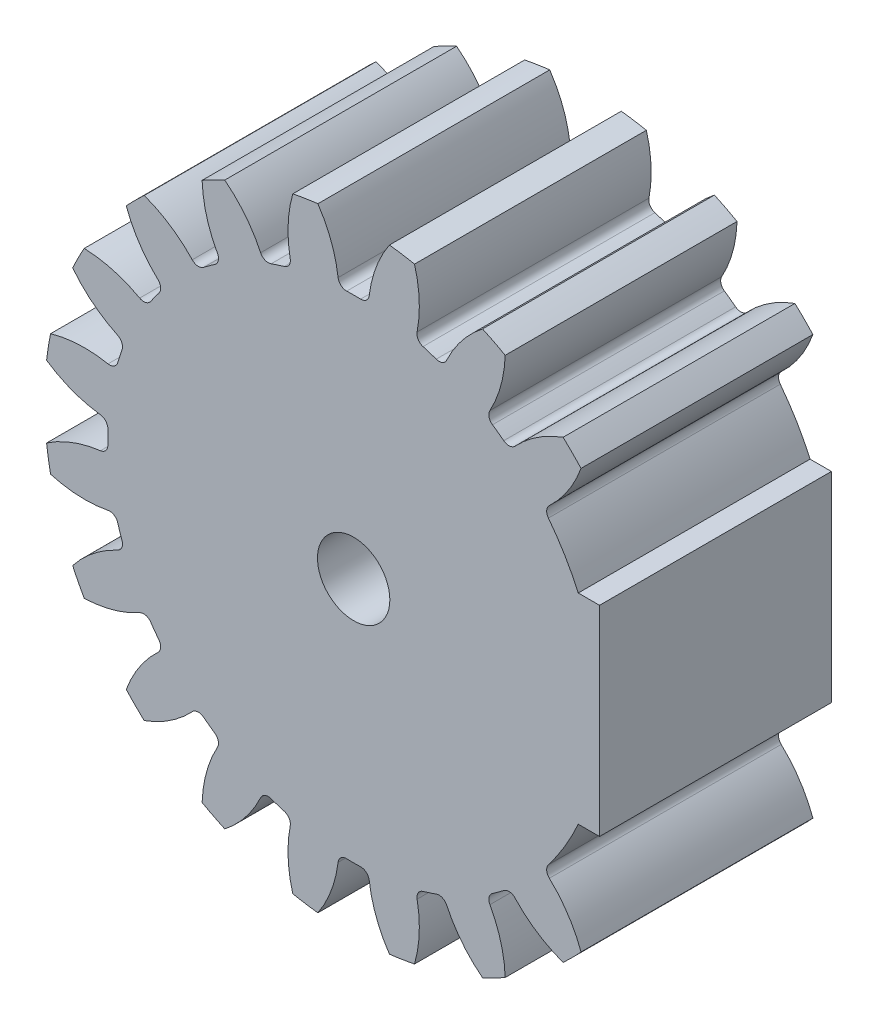
SolidWorks part; units mm, degrees
material "1023 Carbon Steel Sheet (SS)"
ref_plane "Front Plane" through (0, 0, 0) normal (0, 0, 1) x (1, 0, 0)
ref_plane "Top Plane" through (0, 0, 0) normal (0, 1, 0) x (1, 0, 0)
ref_plane "Right Plane" through (0, 0, 0) normal (1, 0, 0) x (0, 0, -1)
sketch "skBase" plane through (0, 0, 0) normal (0, 0, 1) x (1, 0, 0)
  circle A0 centre (0, 0) radius 20
  circle A1 centre (0, 0) radius 22
  circle A2 centre (0, 0) radius 17.5
  dimension "D1" = 40
  dimension "D3" = 4.5
extrude "Base" add sketch "skBase" along normal mid plane 16.5 contours A1
sketch "skToothProfile" plane through (0, 0, 0) normal (0, 0, 1) x (1, 0, 0)
  line L0 (0, 0) -> (0, 22) construction
  line L1 (-1.5692, 19.9383) -> (1.5692, 19.9383) construction
  line L2 (-1.0563, 17.4681) -> (0, 0) construction
  line L3 (0, 15.6271) -> (-2.6287, 22.8493) construction
  line L4 (0, 0) -> (3.4416, 21.7291) construction
  line L5 (1.5692, 19.9383) -> (4.6689, 19.4474) construction
  circle A0 centre (0, 0) radius 22 construction
  arc A1 (-1.0563, 17.4681) -> (-3.258, 22.7681) centre (-9.8105, 16.9387) ccw
  arc A2 (1.0563, 17.4681) -> (3.258, 22.7681) centre (9.8105, 16.9387) cw
  circle A3 centre (0, 0) radius 17.5 construction
  arc A4 (1.0563, 17.4681) -> (-1.0563, 17.4681) centre (0, 0) ccw
  circle A5 centre (0, 0) radius 20 construction
  circle A6 centre (0, 0) radius 22 construction
  circle A7 centre (0, 0) radius 23
  arc A8 (3.258, 22.7681) -> (-3.258, 22.7681) centre (0, 0) ccw
  dimension "D2" = 20
  dimension "D3" = 9
  dimension "D1" = 1
extrude "ToothProfile" cut sketch "skToothProfile" against normal through all and the other way through all
fillet "FilletToothProfile" radius 0.6 2 edges at (1.0563, 17.4681, 0) (-1.0563, 17.4681, 0)
pattern_circular "CirPatternTeeth" count 20 over 360 about axis through (0, 0, 0) along (0, 0, 1) of "ToothProfile", "FilletToothProfile"
sketch "skChaveta" plane through (0, 0, 8.25) normal (0, 0, 1) x (1, 0, 0)
  line L0 (0, 2.575) -> (0, 0) construction
  circle A0 centre (0, 0) radius 2.575
  dimension "D1" = 5.15
extrude "Chaveta" cut sketch "skChaveta" against normal through all
sketch "skRebaixo" plane through (0, 0, 8.25) normal (0, 0, 1) x (1, 0, 0)
  circle A0 centre (0, 0) radius 21.5
  circle A1 centre (0, 0) radius 7.5
  dimension "D1" = 43
  dimension "D2" = 15
sketch "Sketch4" plane through (0, 0, -8.25) normal (0, 0, -1) x (-1, 0, 0)
  circle A0 centre (0, 0) radius 17.5
  arc A5 (-2.5459, 21.8522) -> (-4.3314, 21.5694) centre (0, 0) ccw
  arc A6 (-2.5459, 21.8522) -> (-4.3314, 21.5694) centre (0, 0) ccw
  arc A7 (-18.0189, -1.107) -> (-21.8522, -2.5459) centre (-16.9387, -9.8105) ccw
  arc A8 (-18.0189, -1.107) -> (-21.8522, -2.5459) centre (-16.9387, -9.8105) ccw
  arc A9 (-21.5694, -4.3314) -> (-17.4791, -4.5153) centre (-19.1413, 4.096) ccw
  arc A10 (-21.5694, -4.3314) -> (-17.4791, -4.5153) centre (-19.1413, 4.096) ccw
  arc A127 (-19.996, -9.174) -> (-19.1752, -10.7848) centre (0, 0) ccw
  arc A128 (-19.996, -9.174) -> (-19.1752, -10.7848) centre (0, 0) ccw
  arc A129 (-16.1824, -14.904) -> (-14.904, -16.1824) centre (0, 0) ccw
  arc A130 (-16.1824, -14.904) -> (-14.904, -16.1824) centre (0, 0) ccw
  arc A131 (-10.7848, -19.1752) -> (-9.174, -19.996) centre (0, 0) ccw
  arc A132 (-10.7848, -19.1752) -> (-9.174, -19.996) centre (0, 0) ccw
  arc A133 (-4.3314, -21.5694) -> (-2.5459, -21.8522) centre (0, 0) ccw
  arc A134 (-4.3314, -21.5694) -> (-2.5459, -21.8522) centre (0, 0) ccw
  arc A135 (2.5459, -21.8522) -> (4.3314, -21.5694) centre (0, 0) ccw
  arc A136 (2.5459, -21.8522) -> (4.3314, -21.5694) centre (0, 0) ccw
  arc A137 (9.174, -19.996) -> (10.7848, -19.1752) centre (0, 0) ccw
  arc A138 (9.174, -19.996) -> (10.7848, -19.1752) centre (0, 0) ccw
  arc A139 (14.904, -16.1824) -> (16.1824, -14.904) centre (0, 0) ccw
  arc A140 (14.904, -16.1824) -> (16.1824, -14.904) centre (0, 0) ccw
  arc A141 (19.1752, -10.7848) -> (19.996, -9.174) centre (0, 0) ccw
  arc A142 (19.1752, -10.7848) -> (19.996, -9.174) centre (0, 0) ccw
  arc A143 (21.5694, -4.3314) -> (21.8522, -2.5459) centre (0, 0) ccw
  arc A144 (21.5694, -4.3314) -> (21.8522, -2.5459) centre (0, 0) ccw
  arc A145 (21.8522, 2.5459) -> (21.5694, 4.3314) centre (0, 0) ccw
  arc A146 (21.8522, 2.5459) -> (21.5694, 4.3314) centre (0, 0) ccw
  arc A147 (19.996, 9.174) -> (19.1752, 10.7848) centre (0, 0) ccw
  arc A148 (19.996, 9.174) -> (19.1752, 10.7848) centre (0, 0) ccw
  arc A149 (16.1824, 14.904) -> (14.904, 16.1824) centre (0, 0) ccw
  arc A150 (16.1824, 14.904) -> (14.904, 16.1824) centre (0, 0) ccw
  arc A151 (10.7848, 19.1752) -> (9.174, 19.996) centre (0, 0) ccw
  arc A152 (10.7848, 19.1752) -> (9.174, 19.996) centre (0, 0) ccw
  arc A153 (4.3314, 21.5694) -> (2.5459, 21.8522) centre (0, 0) ccw
  arc A154 (4.3314, 21.5694) -> (2.5459, 21.8522) centre (0, 0) ccw
  arc A155 (-9.174, 19.996) -> (-10.7848, 19.1752) centre (0, 0) ccw
  arc A156 (-9.174, 19.996) -> (-10.7848, 19.1752) centre (0, 0) ccw
  arc A157 (-14.904, 16.1824) -> (-16.1824, 14.904) centre (0, 0) ccw
  arc A158 (-14.904, 16.1824) -> (-16.1824, 14.904) centre (0, 0) ccw
  arc A159 (-19.1752, 10.7848) -> (-19.996, 9.174) centre (0, 0) ccw
  arc A160 (-19.1752, 10.7848) -> (-19.996, 9.174) centre (0, 0) ccw
  arc A161 (-21.5694, 4.3314) -> (-21.8522, 2.5459) centre (0, 0) ccw
  arc A162 (-21.5694, 4.3314) -> (-21.8522, 2.5459) centre (0, 0) ccw
  arc A163 (-4.3314, 21.5694) -> (-4.5153, 17.4791) centre (4.096, 19.1413) ccw
  arc A164 (-4.3314, 21.5694) -> (-4.5153, 17.4791) centre (4.096, 19.1413) ccw
  arc A165 (-4.9352, 16.7897) -> (-4.5153, 17.4791) centre (-5.1044, 17.3653) ccw
  arc A166 (-4.9352, 16.7897) -> (-4.5153, 17.4791) centre (-5.1044, 17.3653) ccw
  arc A167 (-4.9352, 16.7897) -> (-5.8761, 16.484) centre (0, 0) ccw
  arc A168 (-4.9352, 16.7897) -> (-5.8761, 16.484) centre (0, 0) ccw
  arc A169 (-6.621, 16.7949) -> (-5.8761, 16.484) centre (-6.0775, 17.0492) ccw
  arc A170 (-6.621, 16.7949) -> (-5.8761, 16.484) centre (-6.0775, 17.0492) ccw
  arc A171 (-6.621, 16.7949) -> (-9.174, 19.996) centre (-14.5647, 13.0781) ccw
  arc A172 (-6.621, 16.7949) -> (-9.174, 19.996) centre (-14.5647, 13.0781) ccw
  arc A173 (-10.7848, 19.1752) -> (-9.6956, 15.2283) centre (-2.0195, 19.4702) ccw
  arc A174 (-10.7848, 19.1752) -> (-9.6956, 15.2283) centre (-2.0195, 19.4702) ccw
  arc A175 (-9.882, 14.4429) -> (-9.6956, 15.2283) centre (-10.2208, 14.9381) ccw
  arc A176 (-9.882, 14.4429) -> (-9.6956, 15.2283) centre (-10.2208, 14.9381) ccw
  arc A177 (-9.882, 14.4429) -> (-10.6823, 13.8614) centre (0, 0) ccw
  arc A178 (-9.882, 14.4429) -> (-10.6823, 13.8614) centre (0, 0) ccw
  arc A179 (-11.4868, 13.9269) -> (-10.6823, 13.8614) centre (-11.0486, 14.3366) ccw
  arc A180 (-11.4868, 13.9269) -> (-10.6823, 13.8614) centre (-11.0486, 14.3366) ccw
  arc A181 (-11.4868, 13.9269) -> (-14.904, 16.1824) centre (-17.8932, 7.9372) ccw
  arc A182 (-11.4868, 13.9269) -> (-14.904, 16.1824) centre (-17.8932, 7.9372) ccw
  arc A183 (-16.1824, 14.904) -> (-13.9269, 11.4868) centre (-7.9372, 17.8932) ccw
  arc A184 (-16.1824, 14.904) -> (-13.9269, 11.4868) centre (-7.9372, 17.8932) ccw
  arc A185 (-13.8614, 10.6823) -> (-13.9269, 11.4868) centre (-14.3366, 11.0486) ccw
  arc A186 (-13.8614, 10.6823) -> (-13.9269, 11.4868) centre (-14.3366, 11.0486) ccw
  arc A187 (-13.8614, 10.6823) -> (-14.4429, 9.882) centre (0, 0) ccw
  arc A188 (-13.8614, 10.6823) -> (-14.4429, 9.882) centre (0, 0) ccw
  arc A189 (-15.2283, 9.6956) -> (-14.4429, 9.882) centre (-14.9381, 10.2208) ccw
  arc A190 (-15.2283, 9.6956) -> (-14.4429, 9.882) centre (-14.9381, 10.2208) ccw
  arc A191 (-15.2283, 9.6956) -> (-19.1752, 10.7848) centre (-19.4702, 2.0195) ccw
  arc A192 (-15.2283, 9.6956) -> (-19.1752, 10.7848) centre (-19.4702, 2.0195) ccw
  arc A193 (-19.996, 9.174) -> (-16.7949, 6.621) centre (-13.0781, 14.5647) ccw
  arc A194 (-19.996, 9.174) -> (-16.7949, 6.621) centre (-13.0781, 14.5647) ccw
  arc A195 (-16.484, 5.8761) -> (-16.7949, 6.621) centre (-17.0492, 6.0775) ccw
  arc A196 (-16.484, 5.8761) -> (-16.7949, 6.621) centre (-17.0492, 6.0775) ccw
  arc A197 (-16.484, 5.8761) -> (-16.7897, 4.9352) centre (0, 0) ccw
  arc A198 (-16.484, 5.8761) -> (-16.7897, 4.9352) centre (0, 0) ccw
  arc A199 (-17.4791, 4.5153) -> (-16.7897, 4.9352) centre (-17.3653, 5.1044) ccw
  arc A200 (-17.4791, 4.5153) -> (-16.7897, 4.9352) centre (-17.3653, 5.1044) ccw
  arc A201 (-17.4791, 4.5153) -> (-21.5694, 4.3314) centre (-19.1413, -4.096) ccw
  arc A202 (-17.4791, 4.5153) -> (-21.5694, 4.3314) centre (-19.1413, -4.096) ccw
  arc A203 (-21.8522, 2.5459) -> (-18.0189, 1.107) centre (-16.9387, 9.8105) ccw
  arc A204 (-21.8522, 2.5459) -> (-18.0189, 1.107) centre (-16.9387, 9.8105) ccw
  arc A205 (-17.493, 0.4946) -> (-18.0189, 1.107) centre (-18.0928, 0.5116) ccw
  arc A206 (-17.493, 0.4946) -> (-18.0189, 1.107) centre (-18.0928, 0.5116) ccw
  arc A207 (-17.493, 0.4946) -> (-17.493, -0.4946) centre (0, 0) ccw
  arc A208 (-17.493, 0.4946) -> (-17.493, -0.4946) centre (0, 0) ccw
  arc A209 (-18.0189, -1.107) -> (-17.493, -0.4946) centre (-18.0928, -0.5116) ccw
  arc A210 (-18.0189, -1.107) -> (-17.493, -0.4946) centre (-18.0928, -0.5116) ccw
  arc A211 (-16.7897, -4.9352) -> (-17.4791, -4.5153) centre (-17.3653, -5.1044) ccw
  arc A212 (-16.7897, -4.9352) -> (-17.4791, -4.5153) centre (-17.3653, -5.1044) ccw
  arc A213 (-16.7897, -4.9352) -> (-16.484, -5.8761) centre (0, 0) ccw
  arc A214 (-16.7897, -4.9352) -> (-16.484, -5.8761) centre (0, 0) ccw
  arc A215 (-16.7949, -6.621) -> (-16.484, -5.8761) centre (-17.0492, -6.0775) ccw
  arc A216 (-16.7949, -6.621) -> (-16.484, -5.8761) centre (-17.0492, -6.0775) ccw
  arc A217 (-16.7949, -6.621) -> (-19.996, -9.174) centre (-13.0781, -14.5647) ccw
  arc A218 (-16.7949, -6.621) -> (-19.996, -9.174) centre (-13.0781, -14.5647) ccw
  arc A219 (-19.1752, -10.7848) -> (-15.2283, -9.6956) centre (-19.4702, -2.0195) ccw
  arc A220 (-19.1752, -10.7848) -> (-15.2283, -9.6956) centre (-19.4702, -2.0195) ccw
  arc A221 (-14.4429, -9.882) -> (-15.2283, -9.6956) centre (-14.9381, -10.2208) ccw
  arc A222 (-14.4429, -9.882) -> (-15.2283, -9.6956) centre (-14.9381, -10.2208) ccw
  arc A223 (-14.4429, -9.882) -> (-13.8614, -10.6823) centre (0, 0) ccw
  arc A224 (-14.4429, -9.882) -> (-13.8614, -10.6823) centre (0, 0) ccw
  arc A225 (-13.9269, -11.4868) -> (-13.8614, -10.6823) centre (-14.3366, -11.0486) ccw
  arc A226 (-13.9269, -11.4868) -> (-13.8614, -10.6823) centre (-14.3366, -11.0486) ccw
  arc A227 (-13.9269, -11.4868) -> (-16.1824, -14.904) centre (-7.9372, -17.8932) ccw
  arc A228 (-13.9269, -11.4868) -> (-16.1824, -14.904) centre (-7.9372, -17.8932) ccw
  arc A229 (-14.904, -16.1824) -> (-11.4868, -13.9269) centre (-17.8932, -7.9372) ccw
  arc A230 (-14.904, -16.1824) -> (-11.4868, -13.9269) centre (-17.8932, -7.9372) ccw
  arc A231 (-10.6823, -13.8614) -> (-11.4868, -13.9269) centre (-11.0486, -14.3366) ccw
  arc A232 (-10.6823, -13.8614) -> (-11.4868, -13.9269) centre (-11.0486, -14.3366) ccw
  arc A233 (-10.6823, -13.8614) -> (-9.882, -14.4429) centre (0, 0) ccw
  arc A234 (-10.6823, -13.8614) -> (-9.882, -14.4429) centre (0, 0) ccw
  arc A235 (-9.6956, -15.2283) -> (-9.882, -14.4429) centre (-10.2208, -14.9381) ccw
  arc A236 (-9.6956, -15.2283) -> (-9.882, -14.4429) centre (-10.2208, -14.9381) ccw
  arc A237 (-9.6956, -15.2283) -> (-10.7848, -19.1752) centre (-2.0195, -19.4702) ccw
  arc A238 (-9.6956, -15.2283) -> (-10.7848, -19.1752) centre (-2.0195, -19.4702) ccw
  arc A239 (-9.174, -19.996) -> (-6.621, -16.7949) centre (-14.5647, -13.0781) ccw
  arc A240 (-9.174, -19.996) -> (-6.621, -16.7949) centre (-14.5647, -13.0781) ccw
  arc A241 (-5.8761, -16.484) -> (-6.621, -16.7949) centre (-6.0775, -17.0492) ccw
  arc A242 (-5.8761, -16.484) -> (-6.621, -16.7949) centre (-6.0775, -17.0492) ccw
  arc A243 (-5.8761, -16.484) -> (-4.9352, -16.7897) centre (0, 0) ccw
  arc A244 (-5.8761, -16.484) -> (-4.9352, -16.7897) centre (0, 0) ccw
  arc A245 (-4.5153, -17.4791) -> (-4.9352, -16.7897) centre (-5.1044, -17.3653) ccw
  arc A246 (-4.5153, -17.4791) -> (-4.9352, -16.7897) centre (-5.1044, -17.3653) ccw
  arc A247 (-4.5153, -17.4791) -> (-4.3314, -21.5694) centre (4.096, -19.1413) ccw
  arc A248 (-4.5153, -17.4791) -> (-4.3314, -21.5694) centre (4.096, -19.1413) ccw
  arc A249 (-2.5459, -21.8522) -> (-1.107, -18.0189) centre (-9.8105, -16.9387) ccw
  arc A250 (-2.5459, -21.8522) -> (-1.107, -18.0189) centre (-9.8105, -16.9387) ccw
  arc A251 (-0.4946, -17.493) -> (-1.107, -18.0189) centre (-0.5116, -18.0928) ccw
  arc A252 (-0.4946, -17.493) -> (-1.107, -18.0189) centre (-0.5116, -18.0928) ccw
  arc A253 (-0.4946, -17.493) -> (0.4946, -17.493) centre (0, 0) ccw
  arc A254 (-0.4946, -17.493) -> (0.4946, -17.493) centre (0, 0) ccw
  arc A255 (1.107, -18.0189) -> (0.4946, -17.493) centre (0.5116, -18.0928) ccw
  arc A256 (1.107, -18.0189) -> (0.4946, -17.493) centre (0.5116, -18.0928) ccw
  arc A257 (1.107, -18.0189) -> (2.5459, -21.8522) centre (9.8105, -16.9387) ccw
  arc A258 (1.107, -18.0189) -> (2.5459, -21.8522) centre (9.8105, -16.9387) ccw
  arc A259 (4.3314, -21.5694) -> (4.5153, -17.4791) centre (-4.096, -19.1413) ccw
  arc A260 (4.3314, -21.5694) -> (4.5153, -17.4791) centre (-4.096, -19.1413) ccw
  arc A261 (4.9352, -16.7897) -> (4.5153, -17.4791) centre (5.1044, -17.3653) ccw
  arc A262 (4.9352, -16.7897) -> (4.5153, -17.4791) centre (5.1044, -17.3653) ccw
  arc A263 (4.9352, -16.7897) -> (5.8761, -16.484) centre (0, 0) ccw
  arc A264 (4.9352, -16.7897) -> (5.8761, -16.484) centre (0, 0) ccw
  arc A265 (6.621, -16.7949) -> (5.8761, -16.484) centre (6.0775, -17.0492) ccw
  arc A266 (6.621, -16.7949) -> (5.8761, -16.484) centre (6.0775, -17.0492) ccw
  arc A267 (6.621, -16.7949) -> (9.174, -19.996) centre (14.5647, -13.0781) ccw
  arc A268 (6.621, -16.7949) -> (9.174, -19.996) centre (14.5647, -13.0781) ccw
  arc A269 (10.7848, -19.1752) -> (9.6956, -15.2283) centre (2.0195, -19.4702) ccw
  arc A270 (10.7848, -19.1752) -> (9.6956, -15.2283) centre (2.0195, -19.4702) ccw
  arc A271 (9.882, -14.4429) -> (9.6956, -15.2283) centre (10.2208, -14.9381) ccw
  arc A272 (9.882, -14.4429) -> (9.6956, -15.2283) centre (10.2208, -14.9381) ccw
  arc A273 (9.882, -14.4429) -> (10.6823, -13.8614) centre (0, 0) ccw
  arc A274 (9.882, -14.4429) -> (10.6823, -13.8614) centre (0, 0) ccw
  arc A275 (11.4868, -13.9269) -> (10.6823, -13.8614) centre (11.0486, -14.3366) ccw
  arc A276 (11.4868, -13.9269) -> (10.6823, -13.8614) centre (11.0486, -14.3366) ccw
  arc A277 (11.4868, -13.9269) -> (14.904, -16.1824) centre (17.8932, -7.9372) ccw
  arc A278 (11.4868, -13.9269) -> (14.904, -16.1824) centre (17.8932, -7.9372) ccw
  arc A279 (16.1824, -14.904) -> (13.9269, -11.4868) centre (7.9372, -17.8932) ccw
  arc A280 (16.1824, -14.904) -> (13.9269, -11.4868) centre (7.9372, -17.8932) ccw
  arc A281 (13.8614, -10.6823) -> (13.9269, -11.4868) centre (14.3366, -11.0486) ccw
  arc A282 (13.8614, -10.6823) -> (13.9269, -11.4868) centre (14.3366, -11.0486) ccw
  arc A283 (13.8614, -10.6823) -> (14.4429, -9.882) centre (0, 0) ccw
  arc A284 (13.8614, -10.6823) -> (14.4429, -9.882) centre (0, 0) ccw
  arc A285 (15.2283, -9.6956) -> (14.4429, -9.882) centre (14.9381, -10.2208) ccw
  arc A286 (15.2283, -9.6956) -> (14.4429, -9.882) centre (14.9381, -10.2208) ccw
  arc A287 (15.2283, -9.6956) -> (19.1752, -10.7848) centre (19.4702, -2.0195) ccw
  arc A288 (15.2283, -9.6956) -> (19.1752, -10.7848) centre (19.4702, -2.0195) ccw
  arc A289 (19.996, -9.174) -> (16.7949, -6.621) centre (13.0781, -14.5647) ccw
  arc A290 (19.996, -9.174) -> (16.7949, -6.621) centre (13.0781, -14.5647) ccw
  arc A291 (16.484, -5.8761) -> (16.7949, -6.621) centre (17.0492, -6.0775) ccw
  arc A292 (16.484, -5.8761) -> (16.7949, -6.621) centre (17.0492, -6.0775) ccw
  arc A293 (16.484, -5.8761) -> (16.7897, -4.9352) centre (0, 0) ccw
  arc A294 (16.484, -5.8761) -> (16.7897, -4.9352) centre (0, 0) ccw
  arc A295 (17.4791, -4.5153) -> (16.7897, -4.9352) centre (17.3653, -5.1044) ccw
  arc A296 (17.4791, -4.5153) -> (16.7897, -4.9352) centre (17.3653, -5.1044) ccw
  arc A297 (17.4791, -4.5153) -> (21.5694, -4.3314) centre (19.1413, 4.096) ccw
  arc A298 (17.4791, -4.5153) -> (21.5694, -4.3314) centre (19.1413, 4.096) ccw
  arc A299 (21.8522, -2.5459) -> (18.0189, -1.107) centre (16.9387, -9.8105) ccw
  arc A300 (21.8522, -2.5459) -> (18.0189, -1.107) centre (16.9387, -9.8105) ccw
  arc A301 (17.493, -0.4946) -> (18.0189, -1.107) centre (18.0928, -0.5116) ccw
  arc A302 (17.493, -0.4946) -> (18.0189, -1.107) centre (18.0928, -0.5116) ccw
  arc A303 (17.493, -0.4946) -> (17.493, 0.4946) centre (0, 0) ccw
  arc A304 (17.493, -0.4946) -> (17.493, 0.4946) centre (0, 0) ccw
  arc A305 (18.0189, 1.107) -> (17.493, 0.4946) centre (18.0928, 0.5116) ccw
  arc A306 (18.0189, 1.107) -> (17.493, 0.4946) centre (18.0928, 0.5116) ccw
  arc A307 (18.0189, 1.107) -> (21.8522, 2.5459) centre (16.9387, 9.8105) ccw
  arc A308 (18.0189, 1.107) -> (21.8522, 2.5459) centre (16.9387, 9.8105) ccw
  arc A309 (21.5694, 4.3314) -> (17.4791, 4.5153) centre (19.1413, -4.096) ccw
  arc A310 (21.5694, 4.3314) -> (17.4791, 4.5153) centre (19.1413, -4.096) ccw
  arc A311 (-21.8522, -2.5459) -> (-21.5694, -4.3314) centre (0, 0) ccw
  arc A312 (-21.8522, -2.5459) -> (-21.5694, -4.3314) centre (0, 0) ccw
  arc A313 (16.7897, 4.9352) -> (17.4791, 4.5153) centre (17.3653, 5.1044) ccw
  arc A314 (16.7897, 4.9352) -> (17.4791, 4.5153) centre (17.3653, 5.1044) ccw
  arc A315 (16.7897, 4.9352) -> (16.484, 5.8761) centre (0, 0) ccw
  arc A316 (16.7897, 4.9352) -> (16.484, 5.8761) centre (0, 0) ccw
  arc A317 (16.7949, 6.621) -> (16.484, 5.8761) centre (17.0492, 6.0775) ccw
  arc A318 (16.7949, 6.621) -> (16.484, 5.8761) centre (17.0492, 6.0775) ccw
  arc A319 (16.7949, 6.621) -> (19.996, 9.174) centre (13.0781, 14.5647) ccw
  arc A320 (16.7949, 6.621) -> (19.996, 9.174) centre (13.0781, 14.5647) ccw
  arc A321 (19.1752, 10.7848) -> (15.2283, 9.6956) centre (19.4702, 2.0195) ccw
  arc A322 (19.1752, 10.7848) -> (15.2283, 9.6956) centre (19.4702, 2.0195) ccw
  arc A323 (14.4429, 9.882) -> (15.2283, 9.6956) centre (14.9381, 10.2208) ccw
  arc A324 (14.4429, 9.882) -> (15.2283, 9.6956) centre (14.9381, 10.2208) ccw
  arc A325 (14.4429, 9.882) -> (13.8614, 10.6823) centre (0, 0) ccw
  arc A326 (14.4429, 9.882) -> (13.8614, 10.6823) centre (0, 0) ccw
  arc A327 (13.9269, 11.4868) -> (13.8614, 10.6823) centre (14.3366, 11.0486) ccw
  arc A328 (13.9269, 11.4868) -> (13.8614, 10.6823) centre (14.3366, 11.0486) ccw
  arc A329 (13.9269, 11.4868) -> (16.1824, 14.904) centre (7.9372, 17.8932) ccw
  arc A330 (13.9269, 11.4868) -> (16.1824, 14.904) centre (7.9372, 17.8932) ccw
  arc A331 (14.904, 16.1824) -> (11.4868, 13.9269) centre (17.8932, 7.9372) ccw
  arc A332 (14.904, 16.1824) -> (11.4868, 13.9269) centre (17.8932, 7.9372) ccw
  arc A333 (10.6823, 13.8614) -> (11.4868, 13.9269) centre (11.0486, 14.3366) ccw
  arc A334 (10.6823, 13.8614) -> (11.4868, 13.9269) centre (11.0486, 14.3366) ccw
  arc A335 (10.6823, 13.8614) -> (9.882, 14.4429) centre (0, 0) ccw
  arc A336 (10.6823, 13.8614) -> (9.882, 14.4429) centre (0, 0) ccw
  arc A337 (9.6956, 15.2283) -> (9.882, 14.4429) centre (10.2208, 14.9381) ccw
  arc A338 (9.6956, 15.2283) -> (9.882, 14.4429) centre (10.2208, 14.9381) ccw
  arc A339 (9.6956, 15.2283) -> (10.7848, 19.1752) centre (2.0195, 19.4702) ccw
  arc A340 (9.6956, 15.2283) -> (10.7848, 19.1752) centre (2.0195, 19.4702) ccw
  arc A341 (9.174, 19.996) -> (6.621, 16.7949) centre (14.5647, 13.0781) ccw
  arc A342 (9.174, 19.996) -> (6.621, 16.7949) centre (14.5647, 13.0781) ccw
  arc A343 (5.8761, 16.484) -> (6.621, 16.7949) centre (6.0775, 17.0492) ccw
  arc A344 (5.8761, 16.484) -> (6.621, 16.7949) centre (6.0775, 17.0492) ccw
  arc A345 (5.8761, 16.484) -> (4.9352, 16.7897) centre (0, 0) ccw
  arc A346 (5.8761, 16.484) -> (4.9352, 16.7897) centre (0, 0) ccw
  arc A347 (4.5153, 17.4791) -> (4.9352, 16.7897) centre (5.1044, 17.3653) ccw
  arc A348 (4.5153, 17.4791) -> (4.9352, 16.7897) centre (5.1044, 17.3653) ccw
  arc A349 (4.5153, 17.4791) -> (4.3314, 21.5694) centre (-4.096, 19.1413) ccw
  arc A350 (4.5153, 17.4791) -> (4.3314, 21.5694) centre (-4.096, 19.1413) ccw
  arc A351 (2.5459, 21.8522) -> (1.107, 18.0189) centre (9.8105, 16.9387) ccw
  arc A352 (2.5459, 21.8522) -> (1.107, 18.0189) centre (9.8105, 16.9387) ccw
  arc A353 (0.4946, 17.493) -> (1.107, 18.0189) centre (0.5116, 18.0928) ccw
  arc A354 (0.4946, 17.493) -> (1.107, 18.0189) centre (0.5116, 18.0928) ccw
  arc A355 (0.4946, 17.493) -> (-0.4946, 17.493) centre (0, 0) ccw
  arc A356 (0.4946, 17.493) -> (-0.4946, 17.493) centre (0, 0) ccw
  arc A357 (-1.107, 18.0189) -> (-0.4946, 17.493) centre (-0.5116, 18.0928) ccw
  arc A358 (-1.107, 18.0189) -> (-0.4946, 17.493) centre (-0.5116, 18.0928) ccw
  arc A359 (-1.107, 18.0189) -> (-2.5459, 21.8522) centre (-9.8105, 16.9387) ccw
  arc A360 (-1.107, 18.0189) -> (-2.5459, 21.8522) centre (-9.8105, 16.9387) ccw
  dimension "D1" = 0
sketch "Sketch6" plane through (0, 0, -8.25) normal (0, 0, -1) x (-1, 0, 0)
  circle A0 centre (0, 0) radius 20 construction
  dimension "D1" = 40
sketch "Sketch7" plane through (0, 0, -8.25) normal (0, 0, -1) x (-1, 0, 0)
  circle A0 centre (0, 0) radius 17.5
  arc A120 (-2.5459, 21.8522) -> (-4.3314, 21.5694) centre (0, 0) ccw
  arc A121 (-4.3314, 21.5694) -> (-4.5153, 17.4791) centre (4.096, 19.1413) ccw
  arc A122 (-4.9352, 16.7897) -> (-4.5153, 17.4791) centre (-5.1044, 17.3653) ccw
  arc A123 (-4.9352, 16.7897) -> (-5.8761, 16.484) centre (0, 0) ccw
  arc A124 (-6.621, 16.7949) -> (-5.8761, 16.484) centre (-6.0775, 17.0492) ccw
  arc A125 (-6.621, 16.7949) -> (-9.174, 19.996) centre (-14.5647, 13.0781) ccw
  arc A126 (-9.174, 19.996) -> (-10.7848, 19.1752) centre (0, 0) ccw
  arc A127 (-10.7848, 19.1752) -> (-9.6956, 15.2283) centre (-2.0195, 19.4702) ccw
  arc A128 (-9.882, 14.4429) -> (-9.6956, 15.2283) centre (-10.2208, 14.9381) ccw
  arc A129 (-9.882, 14.4429) -> (-10.6823, 13.8614) centre (0, 0) ccw
  arc A130 (-11.4868, 13.9269) -> (-10.6823, 13.8614) centre (-11.0486, 14.3366) ccw
  arc A131 (-11.4868, 13.9269) -> (-14.904, 16.1824) centre (-17.8932, 7.9372) ccw
  arc A132 (-14.904, 16.1824) -> (-16.1824, 14.904) centre (0, 0) ccw
  arc A133 (-16.1824, 14.904) -> (-13.9269, 11.4868) centre (-7.9372, 17.8932) ccw
  arc A134 (-13.8614, 10.6823) -> (-13.9269, 11.4868) centre (-14.3366, 11.0486) ccw
  arc A135 (-13.8614, 10.6823) -> (-14.4429, 9.882) centre (0, 0) ccw
  arc A136 (-15.2283, 9.6956) -> (-14.4429, 9.882) centre (-14.9381, 10.2208) ccw
  arc A137 (-15.2283, 9.6956) -> (-19.1752, 10.7848) centre (-19.4702, 2.0195) ccw
  arc A138 (-19.1752, 10.7848) -> (-19.996, 9.174) centre (0, 0) ccw
  arc A139 (-19.996, 9.174) -> (-16.7949, 6.621) centre (-13.0781, 14.5647) ccw
  arc A140 (-16.484, 5.8761) -> (-16.7949, 6.621) centre (-17.0492, 6.0775) ccw
  arc A141 (-16.484, 5.8761) -> (-16.7897, 4.9352) centre (0, 0) ccw
  arc A142 (-17.4791, 4.5153) -> (-16.7897, 4.9352) centre (-17.3653, 5.1044) ccw
  arc A143 (-17.4791, 4.5153) -> (-21.5694, 4.3314) centre (-19.1413, -4.096) ccw
  arc A144 (-21.5694, 4.3314) -> (-21.8522, 2.5459) centre (0, 0) ccw
  arc A145 (-21.8522, 2.5459) -> (-18.0189, 1.107) centre (-16.9387, 9.8105) ccw
  arc A146 (-17.493, 0.4946) -> (-18.0189, 1.107) centre (-18.0928, 0.5116) ccw
  arc A147 (-17.493, 0.4946) -> (-17.493, -0.4946) centre (0, 0) ccw
  arc A148 (-18.0189, -1.107) -> (-17.493, -0.4946) centre (-18.0928, -0.5116) ccw
  arc A149 (-18.0189, -1.107) -> (-21.8522, -2.5459) centre (-16.9387, -9.8105) ccw
  arc A150 (-21.8522, -2.5459) -> (-21.5694, -4.3314) centre (0, 0) ccw
  arc A151 (-21.5694, -4.3314) -> (-17.4791, -4.5153) centre (-19.1413, 4.096) ccw
  arc A152 (-16.7897, -4.9352) -> (-17.4791, -4.5153) centre (-17.3653, -5.1044) ccw
  arc A153 (-16.7897, -4.9352) -> (-16.484, -5.8761) centre (0, 0) ccw
  arc A154 (-16.7949, -6.621) -> (-16.484, -5.8761) centre (-17.0492, -6.0775) ccw
  arc A155 (-16.7949, -6.621) -> (-19.996, -9.174) centre (-13.0781, -14.5647) ccw
  arc A156 (-19.996, -9.174) -> (-19.1752, -10.7848) centre (0, 0) ccw
  arc A157 (-19.1752, -10.7848) -> (-15.2283, -9.6956) centre (-19.4702, -2.0195) ccw
  arc A158 (-14.4429, -9.882) -> (-15.2283, -9.6956) centre (-14.9381, -10.2208) ccw
  arc A159 (-14.4429, -9.882) -> (-13.8614, -10.6823) centre (0, 0) ccw
  arc A160 (-13.9269, -11.4868) -> (-13.8614, -10.6823) centre (-14.3366, -11.0486) ccw
  arc A161 (-13.9269, -11.4868) -> (-16.1824, -14.904) centre (-7.9372, -17.8932) ccw
  arc A162 (-16.1824, -14.904) -> (-14.904, -16.1824) centre (0, 0) ccw
  arc A163 (-14.904, -16.1824) -> (-11.4868, -13.9269) centre (-17.8932, -7.9372) ccw
  arc A164 (-10.6823, -13.8614) -> (-11.4868, -13.9269) centre (-11.0486, -14.3366) ccw
  arc A165 (-10.6823, -13.8614) -> (-9.882, -14.4429) centre (0, 0) ccw
  arc A166 (-9.6956, -15.2283) -> (-9.882, -14.4429) centre (-10.2208, -14.9381) ccw
  arc A167 (-9.6956, -15.2283) -> (-10.7848, -19.1752) centre (-2.0195, -19.4702) ccw
  arc A168 (-10.7848, -19.1752) -> (-9.174, -19.996) centre (0, 0) ccw
  arc A169 (-9.174, -19.996) -> (-6.621, -16.7949) centre (-14.5647, -13.0781) ccw
  arc A170 (-5.8761, -16.484) -> (-6.621, -16.7949) centre (-6.0775, -17.0492) ccw
  arc A171 (-5.8761, -16.484) -> (-4.9352, -16.7897) centre (0, 0) ccw
  arc A172 (-4.5153, -17.4791) -> (-4.9352, -16.7897) centre (-5.1044, -17.3653) ccw
  arc A173 (-4.5153, -17.4791) -> (-4.3314, -21.5694) centre (4.096, -19.1413) ccw
  arc A174 (-4.3314, -21.5694) -> (-2.5459, -21.8522) centre (0, 0) ccw
  arc A175 (-2.5459, -21.8522) -> (-1.107, -18.0189) centre (-9.8105, -16.9387) ccw
  arc A176 (-0.4946, -17.493) -> (-1.107, -18.0189) centre (-0.5116, -18.0928) ccw
  arc A177 (-0.4946, -17.493) -> (0.4946, -17.493) centre (0, 0) ccw
  arc A178 (1.107, -18.0189) -> (0.4946, -17.493) centre (0.5116, -18.0928) ccw
  arc A179 (1.107, -18.0189) -> (2.5459, -21.8522) centre (9.8105, -16.9387) ccw
  arc A180 (2.5459, -21.8522) -> (4.3314, -21.5694) centre (0, 0) ccw
  arc A181 (4.3314, -21.5694) -> (4.5153, -17.4791) centre (-4.096, -19.1413) ccw
  arc A182 (4.9352, -16.7897) -> (4.5153, -17.4791) centre (5.1044, -17.3653) ccw
  arc A183 (4.9352, -16.7897) -> (5.8761, -16.484) centre (0, 0) ccw
  arc A184 (6.621, -16.7949) -> (5.8761, -16.484) centre (6.0775, -17.0492) ccw
  arc A185 (6.621, -16.7949) -> (9.174, -19.996) centre (14.5647, -13.0781) ccw
  arc A186 (9.174, -19.996) -> (10.7848, -19.1752) centre (0, 0) ccw
  arc A187 (10.7848, -19.1752) -> (9.6956, -15.2283) centre (2.0195, -19.4702) ccw
  arc A188 (9.882, -14.4429) -> (9.6956, -15.2283) centre (10.2208, -14.9381) ccw
  arc A189 (9.882, -14.4429) -> (10.6823, -13.8614) centre (0, 0) ccw
  arc A190 (11.4868, -13.9269) -> (10.6823, -13.8614) centre (11.0486, -14.3366) ccw
  arc A191 (11.4868, -13.9269) -> (14.904, -16.1824) centre (17.8932, -7.9372) ccw
  arc A192 (14.904, -16.1824) -> (16.1824, -14.904) centre (0, 0) ccw
  arc A193 (16.1824, -14.904) -> (13.9269, -11.4868) centre (7.9372, -17.8932) ccw
  arc A194 (13.8614, -10.6823) -> (13.9269, -11.4868) centre (14.3366, -11.0486) ccw
  arc A195 (13.8614, -10.6823) -> (14.4429, -9.882) centre (0, 0) ccw
  arc A196 (15.2283, -9.6956) -> (14.4429, -9.882) centre (14.9381, -10.2208) ccw
  arc A197 (15.2283, -9.6956) -> (19.1752, -10.7848) centre (19.4702, -2.0195) ccw
  arc A198 (19.1752, -10.7848) -> (19.996, -9.174) centre (0, 0) ccw
  arc A199 (19.996, -9.174) -> (16.7949, -6.621) centre (13.0781, -14.5647) ccw
  arc A200 (16.484, -5.8761) -> (16.7949, -6.621) centre (17.0492, -6.0775) ccw
  arc A201 (16.484, -5.8761) -> (16.7897, -4.9352) centre (0, 0) ccw
  arc A202 (17.4791, -4.5153) -> (16.7897, -4.9352) centre (17.3653, -5.1044) ccw
  arc A203 (17.4791, -4.5153) -> (21.5694, -4.3314) centre (19.1413, 4.096) ccw
  arc A204 (21.5694, -4.3314) -> (21.8522, -2.5459) centre (0, 0) ccw
  arc A205 (21.8522, -2.5459) -> (18.0189, -1.107) centre (16.9387, -9.8105) ccw
  arc A206 (17.493, -0.4946) -> (18.0189, -1.107) centre (18.0928, -0.5116) ccw
  arc A207 (17.493, -0.4946) -> (17.493, 0.4946) centre (0, 0) ccw
  arc A208 (18.0189, 1.107) -> (17.493, 0.4946) centre (18.0928, 0.5116) ccw
  arc A209 (18.0189, 1.107) -> (21.8522, 2.5459) centre (16.9387, 9.8105) ccw
  arc A210 (21.8522, 2.5459) -> (21.5694, 4.3314) centre (0, 0) ccw
  arc A211 (21.5694, 4.3314) -> (17.4791, 4.5153) centre (19.1413, -4.096) ccw
  arc A212 (16.7897, 4.9352) -> (17.4791, 4.5153) centre (17.3653, 5.1044) ccw
  arc A213 (16.7897, 4.9352) -> (16.484, 5.8761) centre (0, 0) ccw
  arc A214 (16.7949, 6.621) -> (16.484, 5.8761) centre (17.0492, 6.0775) ccw
  arc A215 (16.7949, 6.621) -> (19.996, 9.174) centre (13.0781, 14.5647) ccw
  arc A216 (19.996, 9.174) -> (19.1752, 10.7848) centre (0, 0) ccw
  arc A217 (19.1752, 10.7848) -> (15.2283, 9.6956) centre (19.4702, 2.0195) ccw
  arc A218 (14.4429, 9.882) -> (15.2283, 9.6956) centre (14.9381, 10.2208) ccw
  arc A219 (14.4429, 9.882) -> (13.8614, 10.6823) centre (0, 0) ccw
  arc A220 (13.9269, 11.4868) -> (13.8614, 10.6823) centre (14.3366, 11.0486) ccw
  arc A221 (13.9269, 11.4868) -> (16.1824, 14.904) centre (7.9372, 17.8932) ccw
  arc A222 (16.1824, 14.904) -> (14.904, 16.1824) centre (0, 0) ccw
  arc A223 (14.904, 16.1824) -> (11.4868, 13.9269) centre (17.8932, 7.9372) ccw
  arc A224 (10.6823, 13.8614) -> (11.4868, 13.9269) centre (11.0486, 14.3366) ccw
  arc A225 (10.6823, 13.8614) -> (9.882, 14.4429) centre (0, 0) ccw
  arc A226 (9.6956, 15.2283) -> (9.882, 14.4429) centre (10.2208, 14.9381) ccw
  arc A227 (9.6956, 15.2283) -> (10.7848, 19.1752) centre (2.0195, 19.4702) ccw
  arc A228 (10.7848, 19.1752) -> (9.174, 19.996) centre (0, 0) ccw
  arc A229 (9.174, 19.996) -> (6.621, 16.7949) centre (14.5647, 13.0781) ccw
  arc A230 (5.8761, 16.484) -> (6.621, 16.7949) centre (6.0775, 17.0492) ccw
  arc A231 (5.8761, 16.484) -> (4.9352, 16.7897) centre (0, 0) ccw
  arc A232 (4.5153, 17.4791) -> (4.9352, 16.7897) centre (5.1044, 17.3653) ccw
  arc A233 (4.5153, 17.4791) -> (4.3314, 21.5694) centre (-4.096, 19.1413) ccw
  arc A234 (4.3314, 21.5694) -> (2.5459, 21.8522) centre (0, 0) ccw
  arc A235 (2.5459, 21.8522) -> (1.107, 18.0189) centre (9.8105, 16.9387) ccw
  arc A236 (0.4946, 17.493) -> (1.107, 18.0189) centre (0.5116, 18.0928) ccw
  arc A237 (0.4946, 17.493) -> (-0.4946, 17.493) centre (0, 0) ccw
  arc A238 (-1.107, 18.0189) -> (-0.4946, 17.493) centre (-0.5116, 18.0928) ccw
  arc A239 (-1.107, 18.0189) -> (-2.5459, 21.8522) centre (-9.8105, 16.9387) ccw
  arc A240 (-2.5459, 21.8522) -> (-4.3314, 21.5694) centre (0, 0) ccw
  arc A241 (-4.3314, 21.5694) -> (-4.5153, 17.4791) centre (4.096, 19.1413) ccw
  arc A242 (-4.9352, 16.7897) -> (-4.5153, 17.4791) centre (-5.1044, 17.3653) ccw
  arc A243 (-4.9352, 16.7897) -> (-5.8761, 16.484) centre (0, 0) ccw
  arc A244 (-6.621, 16.7949) -> (-5.8761, 16.484) centre (-6.0775, 17.0492) ccw
  arc A245 (-6.621, 16.7949) -> (-9.174, 19.996) centre (-14.5647, 13.0781) ccw
  arc A246 (-9.174, 19.996) -> (-10.7848, 19.1752) centre (0, 0) ccw
  arc A247 (-10.7848, 19.1752) -> (-9.6956, 15.2283) centre (-2.0195, 19.4702) ccw
  arc A248 (-9.882, 14.4429) -> (-9.6956, 15.2283) centre (-10.2208, 14.9381) ccw
  arc A249 (-9.882, 14.4429) -> (-10.6823, 13.8614) centre (0, 0) ccw
  arc A250 (-11.4868, 13.9269) -> (-10.6823, 13.8614) centre (-11.0486, 14.3366) ccw
  arc A251 (-11.4868, 13.9269) -> (-14.904, 16.1824) centre (-17.8932, 7.9372) ccw
  arc A252 (-14.904, 16.1824) -> (-16.1824, 14.904) centre (0, 0) ccw
  arc A253 (-16.1824, 14.904) -> (-13.9269, 11.4868) centre (-7.9372, 17.8932) ccw
  arc A254 (-13.8614, 10.6823) -> (-13.9269, 11.4868) centre (-14.3366, 11.0486) ccw
  arc A255 (-13.8614, 10.6823) -> (-14.4429, 9.882) centre (0, 0) ccw
  arc A256 (-15.2283, 9.6956) -> (-14.4429, 9.882) centre (-14.9381, 10.2208) ccw
  arc A257 (-15.2283, 9.6956) -> (-19.1752, 10.7848) centre (-19.4702, 2.0195) ccw
  arc A258 (-19.1752, 10.7848) -> (-19.996, 9.174) centre (0, 0) ccw
  arc A259 (-19.996, 9.174) -> (-16.7949, 6.621) centre (-13.0781, 14.5647) ccw
  arc A260 (-16.484, 5.8761) -> (-16.7949, 6.621) centre (-17.0492, 6.0775) ccw
  arc A261 (-16.484, 5.8761) -> (-16.7897, 4.9352) centre (0, 0) ccw
  arc A262 (-17.4791, 4.5153) -> (-16.7897, 4.9352) centre (-17.3653, 5.1044) ccw
  arc A263 (-17.4791, 4.5153) -> (-21.5694, 4.3314) centre (-19.1413, -4.096) ccw
  arc A264 (-21.5694, 4.3314) -> (-21.8522, 2.5459) centre (0, 0) ccw
  arc A265 (-21.8522, 2.5459) -> (-18.0189, 1.107) centre (-16.9387, 9.8105) ccw
  arc A266 (-17.493, 0.4946) -> (-18.0189, 1.107) centre (-18.0928, 0.5116) ccw
  arc A267 (-17.493, 0.4946) -> (-17.493, -0.4946) centre (0, 0) ccw
  arc A268 (-18.0189, -1.107) -> (-17.493, -0.4946) centre (-18.0928, -0.5116) ccw
  arc A269 (-18.0189, -1.107) -> (-21.8522, -2.5459) centre (-16.9387, -9.8105) ccw
  arc A270 (-21.8522, -2.5459) -> (-21.5694, -4.3314) centre (0, 0) ccw
  arc A271 (-21.5694, -4.3314) -> (-17.4791, -4.5153) centre (-19.1413, 4.096) ccw
  arc A272 (-16.7897, -4.9352) -> (-17.4791, -4.5153) centre (-17.3653, -5.1044) ccw
  arc A273 (-16.7897, -4.9352) -> (-16.484, -5.8761) centre (0, 0) ccw
  arc A274 (-16.7949, -6.621) -> (-16.484, -5.8761) centre (-17.0492, -6.0775) ccw
  arc A275 (-16.7949, -6.621) -> (-19.996, -9.174) centre (-13.0781, -14.5647) ccw
  arc A276 (-19.996, -9.174) -> (-19.1752, -10.7848) centre (0, 0) ccw
  arc A277 (-19.1752, -10.7848) -> (-15.2283, -9.6956) centre (-19.4702, -2.0195) ccw
  arc A278 (-14.4429, -9.882) -> (-15.2283, -9.6956) centre (-14.9381, -10.2208) ccw
  arc A279 (-14.4429, -9.882) -> (-13.8614, -10.6823) centre (0, 0) ccw
  arc A280 (-13.9269, -11.4868) -> (-13.8614, -10.6823) centre (-14.3366, -11.0486) ccw
  arc A281 (-13.9269, -11.4868) -> (-16.1824, -14.904) centre (-7.9372, -17.8932) ccw
  arc A282 (-16.1824, -14.904) -> (-14.904, -16.1824) centre (0, 0) ccw
  arc A283 (-14.904, -16.1824) -> (-11.4868, -13.9269) centre (-17.8932, -7.9372) ccw
  arc A284 (-10.6823, -13.8614) -> (-11.4868, -13.9269) centre (-11.0486, -14.3366) ccw
  arc A285 (-10.6823, -13.8614) -> (-9.882, -14.4429) centre (0, 0) ccw
  arc A286 (-9.6956, -15.2283) -> (-9.882, -14.4429) centre (-10.2208, -14.9381) ccw
  arc A287 (-9.6956, -15.2283) -> (-10.7848, -19.1752) centre (-2.0195, -19.4702) ccw
  arc A288 (-10.7848, -19.1752) -> (-9.174, -19.996) centre (0, 0) ccw
  arc A289 (-9.174, -19.996) -> (-6.621, -16.7949) centre (-14.5647, -13.0781) ccw
  arc A290 (-5.8761, -16.484) -> (-6.621, -16.7949) centre (-6.0775, -17.0492) ccw
  arc A291 (-5.8761, -16.484) -> (-4.9352, -16.7897) centre (0, 0) ccw
  arc A292 (-4.5153, -17.4791) -> (-4.9352, -16.7897) centre (-5.1044, -17.3653) ccw
  arc A293 (-4.5153, -17.4791) -> (-4.3314, -21.5694) centre (4.096, -19.1413) ccw
  arc A294 (-4.3314, -21.5694) -> (-2.5459, -21.8522) centre (0, 0) ccw
  arc A295 (-2.5459, -21.8522) -> (-1.107, -18.0189) centre (-9.8105, -16.9387) ccw
  arc A296 (-0.4946, -17.493) -> (-1.107, -18.0189) centre (-0.5116, -18.0928) ccw
  arc A297 (-0.4946, -17.493) -> (0.4946, -17.493) centre (0, 0) ccw
  arc A298 (1.107, -18.0189) -> (0.4946, -17.493) centre (0.5116, -18.0928) ccw
  arc A299 (1.107, -18.0189) -> (2.5459, -21.8522) centre (9.8105, -16.9387) ccw
  arc A300 (2.5459, -21.8522) -> (4.3314, -21.5694) centre (0, 0) ccw
  arc A301 (4.3314, -21.5694) -> (4.5153, -17.4791) centre (-4.096, -19.1413) ccw
  arc A302 (4.9352, -16.7897) -> (4.5153, -17.4791) centre (5.1044, -17.3653) ccw
  arc A303 (4.9352, -16.7897) -> (5.8761, -16.484) centre (0, 0) ccw
  arc A304 (6.621, -16.7949) -> (5.8761, -16.484) centre (6.0775, -17.0492) ccw
  arc A305 (6.621, -16.7949) -> (9.174, -19.996) centre (14.5647, -13.0781) ccw
  arc A306 (9.174, -19.996) -> (10.7848, -19.1752) centre (0, 0) ccw
  arc A307 (10.7848, -19.1752) -> (9.6956, -15.2283) centre (2.0195, -19.4702) ccw
  arc A308 (9.882, -14.4429) -> (9.6956, -15.2283) centre (10.2208, -14.9381) ccw
  arc A309 (9.882, -14.4429) -> (10.6823, -13.8614) centre (0, 0) ccw
  arc A310 (11.4868, -13.9269) -> (10.6823, -13.8614) centre (11.0486, -14.3366) ccw
  arc A311 (11.4868, -13.9269) -> (14.904, -16.1824) centre (17.8932, -7.9372) ccw
  arc A312 (14.904, -16.1824) -> (16.1824, -14.904) centre (0, 0) ccw
  arc A313 (16.1824, -14.904) -> (13.9269, -11.4868) centre (7.9372, -17.8932) ccw
  arc A314 (13.8614, -10.6823) -> (13.9269, -11.4868) centre (14.3366, -11.0486) ccw
  arc A315 (13.8614, -10.6823) -> (14.4429, -9.882) centre (0, 0) ccw
  arc A316 (15.2283, -9.6956) -> (14.4429, -9.882) centre (14.9381, -10.2208) ccw
  arc A317 (15.2283, -9.6956) -> (19.1752, -10.7848) centre (19.4702, -2.0195) ccw
  arc A318 (19.1752, -10.7848) -> (19.996, -9.174) centre (0, 0) ccw
  arc A319 (19.996, -9.174) -> (16.7949, -6.621) centre (13.0781, -14.5647) ccw
  arc A320 (16.484, -5.8761) -> (16.7949, -6.621) centre (17.0492, -6.0775) ccw
  arc A321 (16.484, -5.8761) -> (16.7897, -4.9352) centre (0, 0) ccw
  arc A322 (17.4791, -4.5153) -> (16.7897, -4.9352) centre (17.3653, -5.1044) ccw
  arc A323 (17.4791, -4.5153) -> (21.5694, -4.3314) centre (19.1413, 4.096) ccw
  arc A324 (21.5694, -4.3314) -> (21.8522, -2.5459) centre (0, 0) ccw
  arc A325 (21.8522, -2.5459) -> (18.0189, -1.107) centre (16.9387, -9.8105) ccw
  arc A326 (17.493, -0.4946) -> (18.0189, -1.107) centre (18.0928, -0.5116) ccw
  arc A327 (17.493, -0.4946) -> (17.493, 0.4946) centre (0, 0) ccw
  arc A328 (18.0189, 1.107) -> (17.493, 0.4946) centre (18.0928, 0.5116) ccw
  arc A329 (18.0189, 1.107) -> (21.8522, 2.5459) centre (16.9387, 9.8105) ccw
  arc A330 (21.8522, 2.5459) -> (21.5694, 4.3314) centre (0, 0) ccw
  arc A331 (21.5694, 4.3314) -> (17.4791, 4.5153) centre (19.1413, -4.096) ccw
  arc A332 (16.7897, 4.9352) -> (17.4791, 4.5153) centre (17.3653, 5.1044) ccw
  arc A333 (16.7897, 4.9352) -> (16.484, 5.8761) centre (0, 0) ccw
  arc A334 (16.7949, 6.621) -> (16.484, 5.8761) centre (17.0492, 6.0775) ccw
  arc A335 (16.7949, 6.621) -> (19.996, 9.174) centre (13.0781, 14.5647) ccw
  arc A336 (19.996, 9.174) -> (19.1752, 10.7848) centre (0, 0) ccw
  arc A337 (19.1752, 10.7848) -> (15.2283, 9.6956) centre (19.4702, 2.0195) ccw
  arc A338 (14.4429, 9.882) -> (15.2283, 9.6956) centre (14.9381, 10.2208) ccw
  arc A339 (14.4429, 9.882) -> (13.8614, 10.6823) centre (0, 0) ccw
  arc A340 (13.9269, 11.4868) -> (13.8614, 10.6823) centre (14.3366, 11.0486) ccw
  arc A341 (13.9269, 11.4868) -> (16.1824, 14.904) centre (7.9372, 17.8932) ccw
  arc A342 (16.1824, 14.904) -> (14.904, 16.1824) centre (0, 0) ccw
  arc A343 (14.904, 16.1824) -> (11.4868, 13.9269) centre (17.8932, 7.9372) ccw
  arc A344 (10.6823, 13.8614) -> (11.4868, 13.9269) centre (11.0486, 14.3366) ccw
  arc A345 (10.6823, 13.8614) -> (9.882, 14.4429) centre (0, 0) ccw
  arc A346 (9.6956, 15.2283) -> (9.882, 14.4429) centre (10.2208, 14.9381) ccw
  arc A347 (9.6956, 15.2283) -> (10.7848, 19.1752) centre (2.0195, 19.4702) ccw
  arc A348 (10.7848, 19.1752) -> (9.174, 19.996) centre (0, 0) ccw
  arc A349 (9.174, 19.996) -> (6.621, 16.7949) centre (14.5647, 13.0781) ccw
  arc A350 (5.8761, 16.484) -> (6.621, 16.7949) centre (6.0775, 17.0492) ccw
  arc A351 (5.8761, 16.484) -> (4.9352, 16.7897) centre (0, 0) ccw
  arc A352 (4.5153, 17.4791) -> (4.9352, 16.7897) centre (5.1044, 17.3653) ccw
  arc A353 (4.5153, 17.4791) -> (4.3314, 21.5694) centre (-4.096, 19.1413) ccw
  arc A354 (4.3314, 21.5694) -> (2.5459, 21.8522) centre (0, 0) ccw
  arc A355 (2.5459, 21.8522) -> (1.107, 18.0189) centre (9.8105, 16.9387) ccw
  arc A356 (0.4946, 17.493) -> (1.107, 18.0189) centre (0.5116, 18.0928) ccw
  arc A357 (0.4946, 17.493) -> (-0.4946, 17.493) centre (0, 0) ccw
  arc A358 (-1.107, 18.0189) -> (-0.4946, 17.493) centre (-0.5116, 18.0928) ccw
  arc A359 (-1.107, 18.0189) -> (-2.5459, 21.8522) centre (-9.8105, 16.9387) ccw
  dimension "D1" = 0
extrude "Cut-Extrude1" cut sketch "Sketch7" against normal blind 16.5 contours A266 A0 A262 A263 A264 A265 | A272 A0 A268 A269 A270 A271 | A278 A0 A274 A275 A276 A277 | A260 A0 A256 A257 A258 A259
sketch "Sketch8" plane through (0, 0, -8.25) normal (0, 0, -1) x (-1, 0, 0)
  line L1 (-17.5, 7.125) -> (-2.575, 7.125)
  line L2 (-17.5, 7.125) -> (-17.5, -7.125)
  line L3 (-17.5, -7.125) -> (-2.575, -7.125)
  line L4 (-2.575, 7.125) -> (-2.575, -7.125)
  circle A0 centre (0, 0) radius 2.575 construction
  arc A1 (-13.8614, 10.6823) -> (-13.8614, -10.6823) centre (0, 0) ccw construction
  point P6 (-2.575, 0)
  dimension "D1" = 14.25
extrude "Boss-Extrude1" add sketch "Sketch8" against normal up to surface (16.5 mm away) up to face at (2.575, 0, 8.25)
equation "\"Module\"= 2mm"
equation "\"Number_Of_Teeth\"= 20"
equation "\"D1@skBase\"=\"Module\" * \"Number_Of_Teeth\""
equation "\"D2@skBase\"=\"Module\""
equation "\"D3@skBase\"=\"Module\" * if( \"Module\" >=1.25, 2.25, 2.4)"
equation "\"Pressure_Angle\"= 20deg"
equation "\"D2@skToothProfile\"=\"Pressure_Angle\""
equation "\"D3@skToothProfile\"=180 / \"Number_Of_Teeth\""
equation "\"D1@FilletToothProfile\"= 0.3 * \"Module\""
equation "\"D1@CirPatternTeeth\"=\"Number_Of_Teeth\""
equation "\"Width\" = 16.5mm"
equation "\"D1@Base\"=\"Width\""
equation "\"D1@Cut-Extrude1\"=\"Width\""
